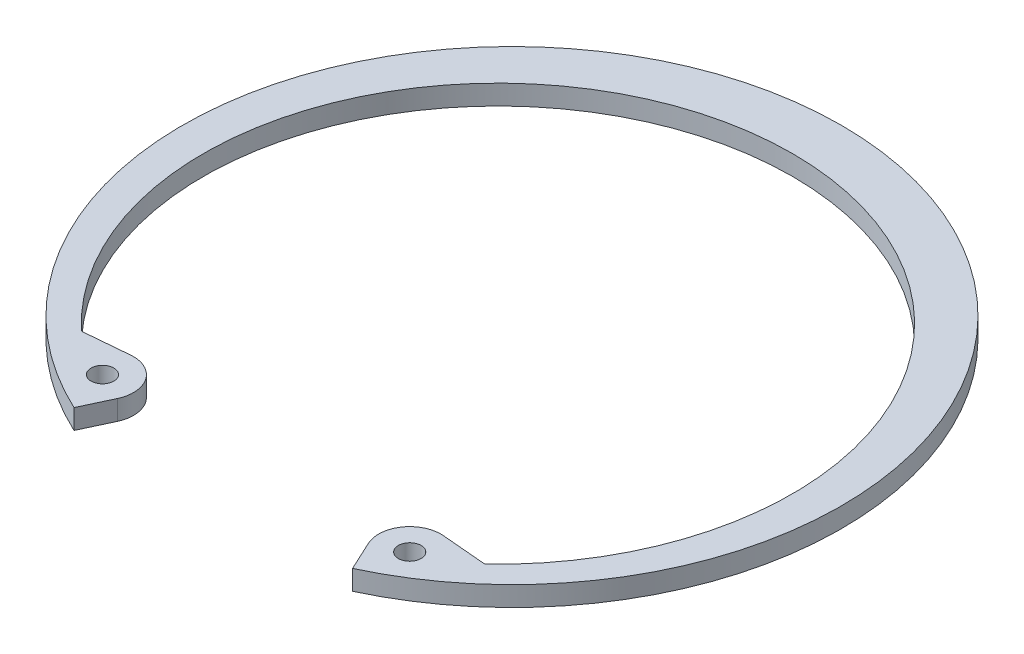
SolidWorks part; units mm, degrees
material "Cast Carbon Steel"
ref_plane "Front" through (0, 0, 0) normal (0, 0, 1) x (1, 0, 0)
ref_plane "Top" through (0, 0, 0) normal (0, 1, 0) x (1, 0, 0)
ref_plane "Right" through (0, 0, 0) normal (1, 0, 0) x (0, 0, -1)
sketch "Sketch2" plane through (0, 0, 0) normal (0, 1, 0) x (1, 0, 0)
  line L0 (0, 0) -> (0, -46.0121) construction
  line L1 (-28.1521, -31.9497) -> (-30.419, -34.5224) construction
  line L2 (19.4456, -41.7011) -> (17.514, -37.5589)
  line L3 (-19.4456, -41.7011) -> (-17.514, -37.5589)
  line L4 (0, 39.1795) -> (0, 46.0121) construction
  line L5 (28.1521, -31.9497) -> (21.829, -31.3965)
  line L6 (-28.1521, -31.9497) -> (-21.829, -31.3965)
  line L7 (19.2146, -31.9997) -> (0.7532, -43.085) construction
  line L8 (0.7532, -43.085) -> (5.225, -50.5324) construction
  line L9 (5.225, -50.5324) -> (23.6864, -39.447) construction
  line L10 (19.2146, -31.9997) -> (23.6864, -39.447) construction
  line L11 (21.4505, -35.7233) -> (17.514, -37.5589) construction
  line L12 (21.4505, -35.7233) -> (23.6864, -39.447) construction
  line L13 (19.2146, -31.9997) -> (-19.2146, -31.9997) construction
  line L14 (-19.2146, -31.9997) -> (-23.6864, -39.447) construction
  line L15 (-46.0121, 0) -> (46.0121, 0) construction
  arc A1 (19.4456, -41.7011) -> (-19.4456, -41.7011) centre (0, 0) ccw
  arc A2 (28.1521, -31.9497) -> (-28.1521, -31.9497) centre (0, -1.9562) ccw
  circle A3 centre (0, 0) radius 46.0121 construction
  arc A4 (17.514, -37.5589) -> (21.829, -31.3965) centre (21.4505, -35.7233) cw
  arc A5 (-17.514, -37.5589) -> (-21.829, -31.3965) centre (-21.4505, -35.7233) ccw
  circle A6 centre (21.4505, -35.7233) radius 1.5875
  circle A7 centre (-21.4505, -35.7233) radius 1.5875
  arc A8 (28.1521, -31.9497) -> (-28.1521, -31.9497) centre (0, -1.9562) cw construction
  circle A9 centre (0, 0) radius 33.4645 construction
  point P5 (21.4505, -35.7233)
  point P10 (19.2146, -31.9997)
  dimension "D1" = 60
  dimension "D2" = 60
  dimension "L" = 66.929
  dimension "R" = 3.175
  dimension "Df" = 92.0242
  dimension "H" = 8.6868
  dimension "Angle" = 25
  dimension "Sec. Max" = 6.8326
  dimension "Sec. Min" = 3.429
extrude "Extrude1" add sketch "Sketch2" against normal blind 2.7686
fillet "Fillet1" radius 0.254 2 edges at (-28.1521, -1.3843, 31.9497) (28.1521, -1.3843, 31.9497)
sketch "Sketch3" plane through (0, 0, 0) normal (1, 0, 0) x (0, 0, -1)
  line L0 (-41.275, -28.9306) -> (-41.275, -2.9083)
  line L1 (-41.275, -2.9083) -> (-43.7642, -2.9083)
  line L2 (-43.7642, -2.9083) -> (-43.7642, 0.1397)
  line L3 (-43.7642, 0.1397) -> (-41.275, 0.1397)
  line L4 (-41.275, 0.1397) -> (-41.275, 4.2926)
  line L5 (-41.275, -28.9306) -> (-46.2534, -28.9306)
  line L6 (-41.275, -2.9083) -> (0, -2.9083) construction
  line L7 (-41.275, 4.2926) -> (-46.2534, 4.2926)
  line L8 (0, 130.3401) -> (0, 164.6301) construction
  line L9 (0, -2.9083) -> (0, 0.1397) construction
  line L10 (0, 0.1397) -> (-41.275, 0.1397) construction
  line L11 (-43.7642, -1.3843) -> (0, -1.3843) construction
  line L12 (0, -135.0899) -> (0, 130.3401) construction
  line L13 (-31.8714, -2.7686) -> (39.1795, -2.7686) construction
  line L14 (-46.2534, -28.9306) -> (-46.2534, 4.2926)
  dimension "Shaft Lg" = 33.2232
  dimension "D1" = 1.3843
  dimension "D2" = 2.4892
  dimension "D4" = 2.4892
  dimension "D3" = 4.1529
revolve "Revolve1" [suppressed] add sketch "Sketch3" angle 360 about L8
delete or keep bodies "Body-Delete1" [suppressed] type delete bodies bodies 116
equation "\"D3@Sketch3\" = \"Shaft Lg@Sketch3\"/8"
equation "\"Shaft Lg@Sketch3\" = \"D1@Extrude1\"*12"
equation "\"D1@Sketch3\" = \"D1@Extrude1\"/2"
equation "\"D2@Sketch3\" = \"D4@Sketch3\""
